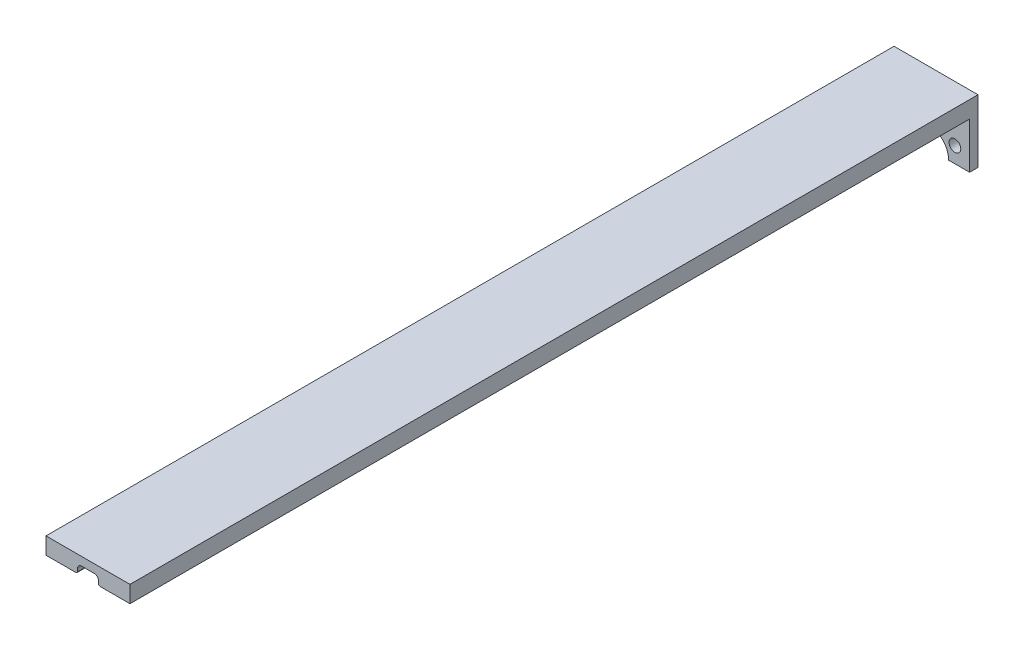
SolidWorks part; units mm, degrees
material "Alloy Steel"
ref_plane "Front Plane" through (0, 0, 0) normal (0, 0, 1) x (1, 0, 0)
ref_plane "Top Plane" through (0, 0, 0) normal (0, 1, 0) x (1, 0, 0)
ref_plane "Right Plane" through (0, 0, 0) normal (1, 0, 0) x (0, 0, -1)
sketch "Sketch2" plane through (0, 0, 0) normal (0, 0, 1) x (1, 0, 0)
  line L0 (-12.7, 0) -> (-6.35, 0)
  line L1 (6.35, 0) -> (12.7, 0)
  line L2 (12.7, 0) -> (12.7, 19.05)
  line L3 (-12.7, 19.05) -> (-12.7, 0)
  line L4 (-12.7, 19.05) -> (12.7, 19.05)
  circle A0 centre (0, 0) radius 9.525 construction
  circle A1 centre (0, 0) radius 12.7 construction
  circle A2 centre (0, -9.525) radius 1.778 construction
  circle A3 centre (-8.2489, 4.7625) radius 1.778
  circle A4 centre (8.2489, 4.7625) radius 1.778
  circle A5 centre (0, 0) radius 6.35 construction
  arc A6 (-6.35, 0) -> (6.35, 0) centre (0, 0) cw
  point P12 (0, 0)
  dimension "D1" = 19.05
  dimension "D2" = 25.4
  dimension "D3" = 3.556
  dimension "D5" = 12.7
  dimension "D6" = 19.05
  dimension "D4" = 3
extrude "Boss-Extrude1" add sketch "Sketch2" along normal blind 2.54
sketch "Sketch3" plane through (0, 0, 2.54) normal (0, 0, 1) x (1, 0, 0)
  line L0 (-12.7, 19.05) -> (-12.7, 13.97)
  line L1 (-12.7, 19.05) -> (-12.7, 0) construction
  line L4 (-12.7, 13.97) -> (-3.683, 13.97)
  line L5 (-3.175, 14.478) -> (-3.175, 15.24)
  line L6 (-12.7, 19.05) -> (12.7, 19.05)
  line L7 (12.7, 19.05) -> (-12.7, 19.05) construction
  line L8 (-1.905, 16.51) -> (1.905, 16.51)
  line L9 (0, 19.05) -> (0, 0) construction
  line L10 (3.175, 14.478) -> (3.175, 15.24)
  line L12 (12.7, 13.97) -> (3.683, 13.97)
  line L14 (12.7, 19.05) -> (12.7, 13.97)
  line L15 (12.7, 0) -> (12.7, 19.05) construction
  arc A0 (-3.175, 15.24) -> (-1.905, 16.51) centre (-1.905, 15.24) cw
  arc A1 (3.175, 15.24) -> (1.905, 16.51) centre (1.905, 15.24) ccw
  arc A2 (3.175, 14.478) -> (3.683, 13.97) centre (3.683, 14.478) ccw
  arc A3 (-3.683, 13.97) -> (-3.175, 14.478) centre (-3.683, 14.478) ccw
  point P17 (0, 16.51)
  point P20 (-3.175, 16.51)
  point P22 (0, 19.05)
  point P25 (3.175, 16.51)
  point P28 (3.175, 13.97)
  point P31 (-3.175, 13.97)
  dimension "D3" = 1.27
  dimension "D4" = 0.508
  dimension "D1" = 5.08
  dimension "D2" = 6.35
  dimension "D5" = 2.54
extrude "Boss-Extrude2" add sketch "Sketch3" along normal blind 254
